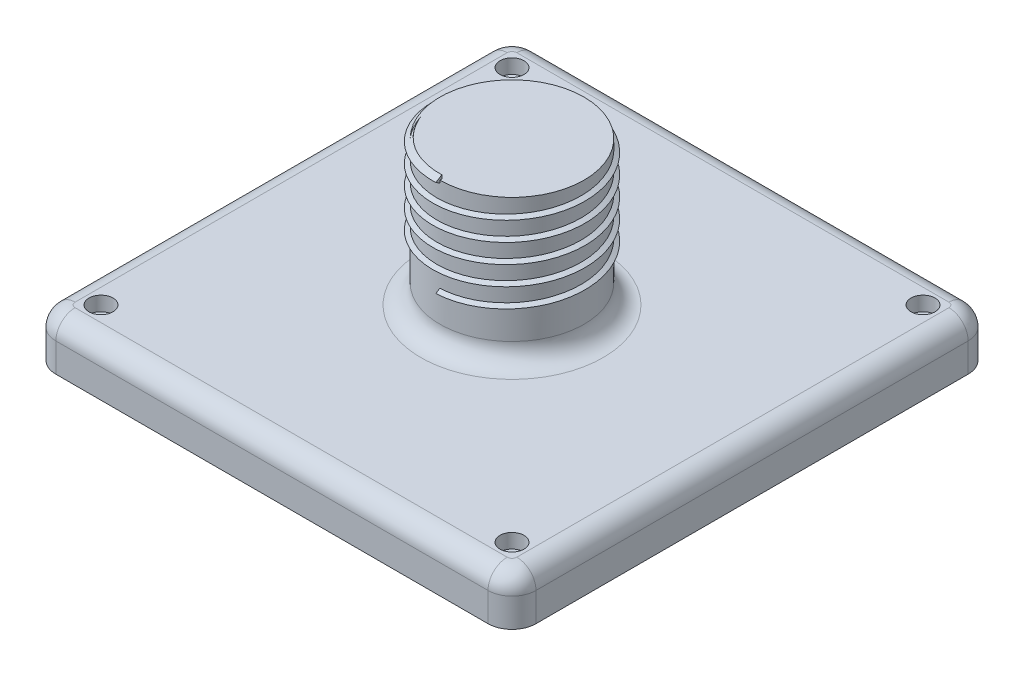
SolidWorks part; units mm, degrees
ref_plane "Front Plane" through (0, 0, 0) normal (0, 0, 1) x (1, 0, 0)
ref_plane "Top Plane" through (0, 0, 0) normal (0, 1, 0) x (1, 0, 0)
ref_plane "Right Plane" through (0, 0, 0) normal (1, 0, 0) x (0, 0, -1)
sketch "Sketch1" plane through (0, 0, 0) normal (0, 1, 0) x (1, 0, 0)
  line L0 (-50, 0) -> (50, 0) construction
  line L1 (45, -50) -> (-45, -50)
  line L2 (50, -45) -> (50, 45)
  line L3 (45, 50) -> (-45, 50)
  line L4 (-50, -45) -> (-50, 45)
  line L5 (50, -50) -> (-50, 50) construction
  line L6 (50, 50) -> (-50, -50) construction
  line L7 (0, 50) -> (0, -50) construction
  circle A0 centre (-42.8043, 42.8043) radius 1
  circle A1 centre (42.8043, -42.8043) radius 1
  circle A5 centre (42.8043, 42.8043) radius 1
  circle A6 centre (-42.8043, -42.8043) radius 1
  arc A7 (-45, -50) -> (-50, -45) centre (-45, -45) cw
  arc A8 (45, -50) -> (50, -45) centre (45, -45) ccw
  arc A9 (50, 45) -> (45, 50) centre (45, 45) ccw
  arc A10 (-45, 50) -> (-50, 45) centre (-45, 45) ccw
  point P0 (0, 0)
  point P18 (0, 0)
  dimension "D2" = 5
  dimension "D3" = 2
  dimension "D4" = 90
extrude "base" add sketch "Sketch1" along normal blind 10
fillet "base redondedo" radius 4 8 edges at (48.5355, 10, 48.5355) (0, 10, 50) (-48.5355, 10, 48.5355) (-50, 10, 0) (-48.5355, 10, -48.5355) (0, 10, -50) (48.5355, 10, -48.5355) (50, 10, 0)
sketch "Sketch4" plane through (0, 10, 0) normal (0, 1, 0) x (1, 0, 0)
  circle A0 centre (-42.8043, 42.8043) radius 2.5
  circle A1 centre (42.8043, 42.8043) radius 2.5
  circle A2 centre (42.8043, -42.8043) radius 2.5
  circle A3 centre (-42.8043, -42.8043) radius 2.5
  dimension "D1" = 5
extrude "Cut-Extrude1" cut sketch "Sketch4" against normal blind 3
sketch "Sketch5" plane through (0, 10, 0) normal (0, 1, 0) x (1, 0, 0)
  circle A0 centre (0, 0) radius 15
  dimension "D1" = 30
extrude "saliente" add sketch "Sketch5" along normal blind 30
sketch "Sketch7" plane through (0, 40, 0) normal (0, 1, 0) x (1, 0, 0)
  circle A0 centre (0, 0) radius 15
curve "linearosca" pitch 4 height 20 turns 5
ref_plane "Plane1" through (0, 40, 15) normal (-0.9991, -0.0424, 0) x (0, 0, 1)
sketch "Sketch15" plane through (0, 40, 15) normal (-0.9991, -0.0424, 0) x (0, 0, 1)
  line L1 (-0.433, 0.75) -> (-0.433, -0.75)
  line L2 (-0.433, -0.75) -> (0.866, 0)
  line L3 (0.866, 0) -> (-0.433, 0.75)
  circle A0 centre (0, 0) radius 0.433 construction
  point P1 (0, 0.9114)
  point P7 (0.866, 0)
  dimension "D1" = 1.5
sketch "Sketch16" plane through (0, 40, 15) normal (-0.9991, -0.0424, 0) x (0, 0, 1)
sweep "rosca" add profiles "Sketch15" path "linearosca"
fillet "redondeo union base y saliente" radius 4 1 edges at (0, 10, -15)
